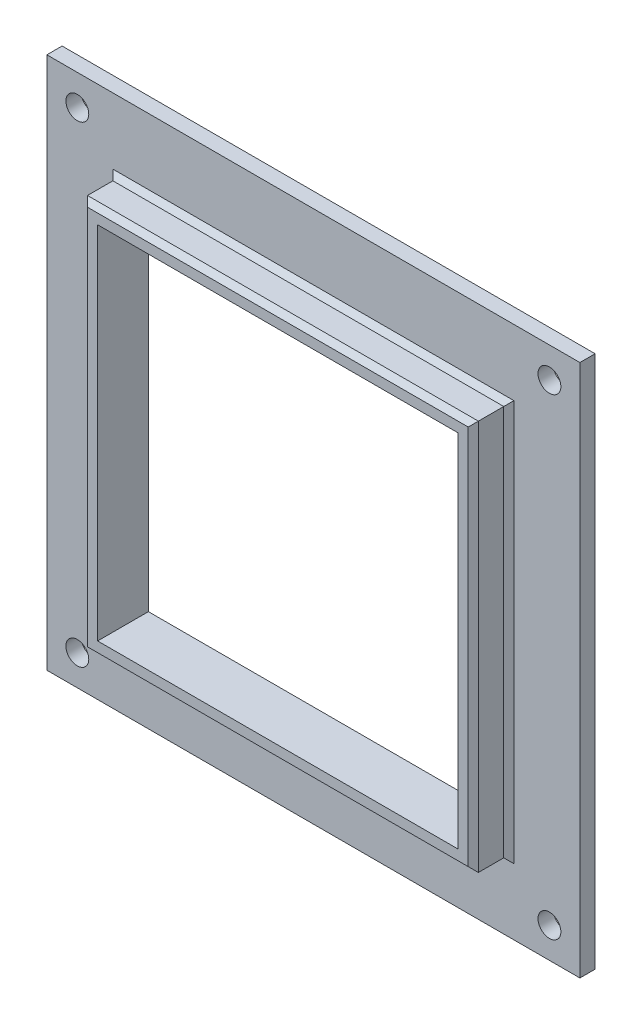
SolidWorks part; units mm, degrees
ref_plane "Спереди" through (0, 0, 0) normal (0, 0, 1) x (1, 0, 0)
ref_plane "Сверху" through (0, 0, 0) normal (0, 1, 0) x (1, 0, 0)
ref_plane "Справа" through (0, 0, 0) normal (1, 0, 0) x (0, 0, -1)
sketch "Эскиз1" plane through (0, 0, 0) normal (0, 0, 1) x (1, 0, 0)
  line L0 (0, 0) -> (71, 0)
  line L1 (0, 0) -> (0, 71)
  line L2 (71, 0) -> (71, 71)
  line L3 (0, 71) -> (71, 71)
  line L4 (-17, 88) -> (88, 88)
  line L5 (-17, 88) -> (-17, -17)
  line L6 (88, 88) -> (88, -17)
  line L7 (-17, -17) -> (88, -17)
  line L8 (35.5, 71) -> (35.5, 0) construction
  line L9 (71, 35.5) -> (0, 35.5) construction
  line L10 (35.5, 88) -> (35.5, -17) construction
  line L11 (88, 35.5) -> (-17, 35.5) construction
  dimension "D1" = 71
  dimension "D2" = 71
  dimension "D3" = 17
  dimension "D4" = 17
extrude "Бобышка-Вытянуть1" add sketch "Эскиз1" along normal blind 3
sketch "Эскиз2" plane through (0, 0, 3) normal (0, 0, 1) x (1, 0, 0)
  line L0 (71, 0) -> (71, 71) construction
  line L1 (0, 0) -> (71, 0) construction
  line L2 (0, 71) -> (0, 0) construction
  line L3 (71, 71) -> (0, 71) construction
  line L4 (71, 0) -> (71, 71)
  line L5 (0, 0) -> (71, 0)
  line L6 (0, 71) -> (0, 0)
  line L7 (71, 71) -> (0, 71)
  line L8 (-3, 74) -> (74, 74)
  line L9 (-3, 74) -> (-3, -3)
  line L10 (74, 74) -> (74, -3)
  line L11 (-3, -3) -> (74, -3)
  dimension "D1" = 3
  dimension "D2" = 3
  dimension "D3" = 3
  dimension "D4" = 3
extrude "Бобышка-Вытянуть2" add sketch "Эскиз2" along normal blind 7
chamfer "Фаска1" distance 1 angle 45 8 edges at (35.5, 74, 3) (-3, 35.5, 3) (74, 35.5, 3) (35.5, -3, 3) (35.5, 74, 10) (-3, 35.5, 10) (35.5, -3, 10) (74, 35.5, 10)
sketch "Эскиз3" plane through (0, 0, 0) normal (0, 0, -1) x (-1, 0, 0)
  line L0 (17, 35.5) -> (-88, 35.5) construction
  line L1 (17, 88) -> (17, -17) construction
  line L2 (-88, -17) -> (-88, 88) construction
  line L3 (-35.5, -17) -> (-35.5, 88) construction
  line L4 (17, -17) -> (-88, -17) construction
  line L5 (-88, 88) -> (17, 88) construction
sketch "Эскиз4" plane through (0, 0, 3) normal (0, 0, 1) x (1, 0, 0)
  line L0 (-11, 82) -> (82, 82) construction
  line L1 (-11, 82) -> (-11, -11) construction
  line L2 (82, 82) -> (82, -11) construction
  line L3 (-11, -11) -> (82, -11) construction
  line L4 (88, 88) -> (-17, 88) construction
  line L5 (-17, 88) -> (-17, -17) construction
  line L6 (88, -17) -> (88, 88) construction
  line L7 (-17, -17) -> (88, -17) construction
  circle A0 centre (-11, 82) radius 2.25
  circle A1 centre (82, 82) radius 2.25
  circle A2 centre (82, -11) radius 2.25
  circle A3 centre (-11, -11) radius 2.25
  dimension "D1" = 4.5
  dimension "D2" = 4.5
  dimension "D3" = 4.5
  dimension "D4" = 4.5
  dimension "D5" = 6
  dimension "D6" = 6
  dimension "D7" = 6
  dimension "D8" = 6
extrude "Вырез-Вытянуть1" cut sketch "Эскиз4" against normal through all
